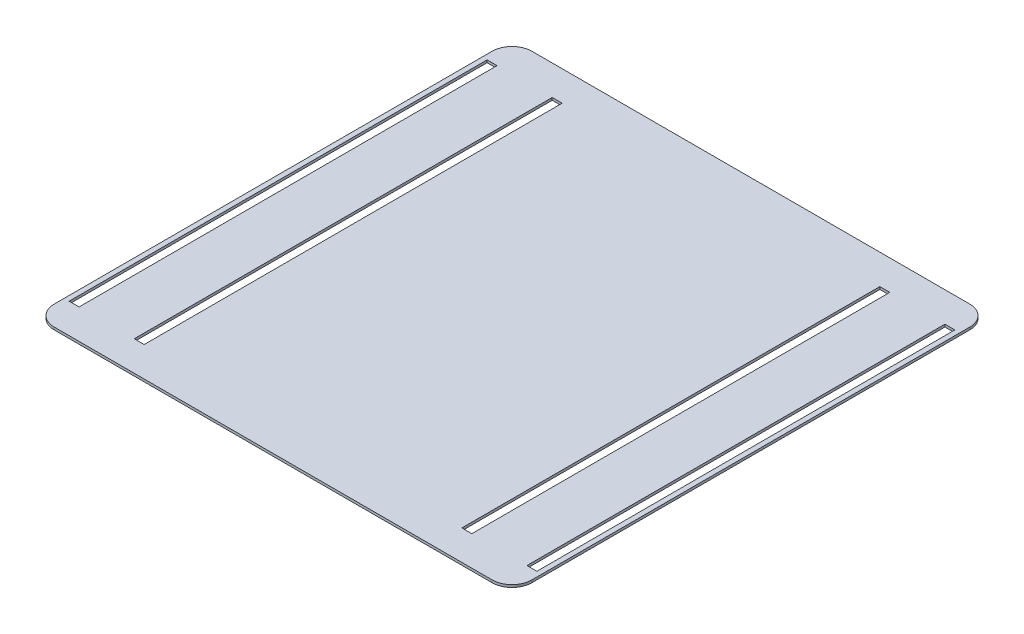
SolidWorks part; units mm, degrees
material "6061 Alloy"
ref_plane "Front Plane" through (0, 0, 0) normal (0, 0, 1) x (1, 0, 0)
ref_plane "Top Plane" through (0, 0, 0) normal (0, 1, 0) x (1, 0, 0)
ref_plane "Right Plane" through (0, 0, 0) normal (1, 0, 0) x (0, 0, -1)
sketch "Sketch1" plane through (0, 0, 0) normal (0, 1, 0) x (1, 0, 0)
  line L1 (-304.8, -304.8) -> (304.8, -304.8)
  line L2 (-304.8, -304.8) -> (-304.8, 304.8)
  line L3 (-304.8, 304.8) -> (304.8, 304.8)
  line L4 (304.8, -304.8) -> (304.8, 304.8)
  line L5 (-304.8, -304.8) -> (304.8, 304.8) construction
  line L6 (-304.8, 304.8) -> (304.8, -304.8) construction
  point P0 (0, 0)
  dimension "D1" = 609.6
  dimension "D2" = 609.6
extrude "Boss-Extrude1" add sketch "Sketch1" along normal blind 3.175
fillet "Fillet1" radius 25.4 4 edges at (-304.8, 1.5875, -304.8) (304.8, 1.5875, -304.8) (-304.8, 1.5875, 304.8) (304.8, 1.5875, 304.8)
sketch "Sketch2" plane through (0, 3.175, 0) normal (0, 1, 0) x (1, 0, 0)
  line L0 (-304.8, 279.4) -> (-304.8, -279.4) construction
  line L1 (-304.8, 279.4) -> (-304.8, -279.4)
  line L2 (-221.742, -304.8) -> (-221.742, 304.8) construction
  line L3 (-196.342, -304.8) -> (-196.342, 304.8) construction
  line L4 (-279.4, -304.8) -> (-279.4, 304.8) construction
  line L5 (-221.742, -304.8) -> (-221.742, 304.8)
  line L6 (-196.342, -304.8) -> (-196.342, 304.8)
  line L7 (-279.4, -304.8) -> (-279.4, 304.8)
  line L10 (0, -304.8) -> (0, 304.8) construction
  line L11 (-279.4, -304.8) -> (279.4, -304.8) construction
  line L12 (279.4, 304.8) -> (-279.4, 304.8) construction
  line L13 (-221.742, 304.8) -> (-196.342, 304.8)
  line L14 (-298.45, 266.7) -> (-285.75, 266.7)
  line L15 (-298.45, 266.7) -> (-298.45, -266.7)
  line L16 (-298.45, -266.7) -> (-285.75, -266.7)
  line L17 (-285.75, 266.7) -> (-285.75, -266.7)
  line L18 (-221.742, -304.8) -> (-196.342, -304.8)
  line L19 (215.392, -266.7) -> (215.392, 266.7)
  line L20 (-202.692, -266.7) -> (-215.392, -266.7)
  line L21 (-202.692, -266.7) -> (-202.692, 266.7)
  line L22 (-202.692, 266.7) -> (-215.392, 266.7)
  line L23 (-215.392, -266.7) -> (-215.392, 266.7)
  line L24 (202.692, 266.7) -> (215.392, 266.7)
  line L25 (202.692, -266.7) -> (202.692, 266.7)
  line L26 (202.692, -266.7) -> (215.392, -266.7)
  line L27 (221.742, -304.8) -> (196.342, -304.8)
  line L28 (285.75, 266.7) -> (285.75, -266.7)
  line L29 (298.45, -266.7) -> (285.75, -266.7)
  line L30 (298.45, 266.7) -> (298.45, -266.7)
  line L31 (298.45, 266.7) -> (285.75, 266.7)
  line L32 (221.742, 304.8) -> (196.342, 304.8)
  line L33 (279.4, -304.8) -> (279.4, 304.8)
  line L34 (196.342, -304.8) -> (196.342, 304.8)
  line L35 (221.742, -304.8) -> (221.742, 304.8)
  line L36 (304.8, 279.4) -> (304.8, -279.4)
  arc A0 (-304.8, -279.4) -> (-279.4, -304.8) centre (-279.4, -279.4) ccw
  arc A1 (-304.8, 279.4) -> (-279.4, 304.8) centre (-279.4, 279.4) cw
  arc A2 (304.8, 279.4) -> (279.4, 304.8) centre (279.4, 279.4) ccw
  arc A3 (304.8, -279.4) -> (279.4, -304.8) centre (279.4, -279.4) cw
  dimension "D1" = 12.7
  dimension "D2" = 6.35
  dimension "D3" = 38.1
  dimension "D4" = 38.1
  dimension "D5" = 12.7
  dimension "D6" = 38.1
  dimension "D7" = 38.1
  dimension "D8" = 6.35
extrude "Cut-Extrude1" cut sketch "Sketch2" against normal blind 3.175 contours L25 L26 L19 L24 | L21 L20 L23 L22 | L15 L16 L17 L14 | L28 L29 L30 L31
